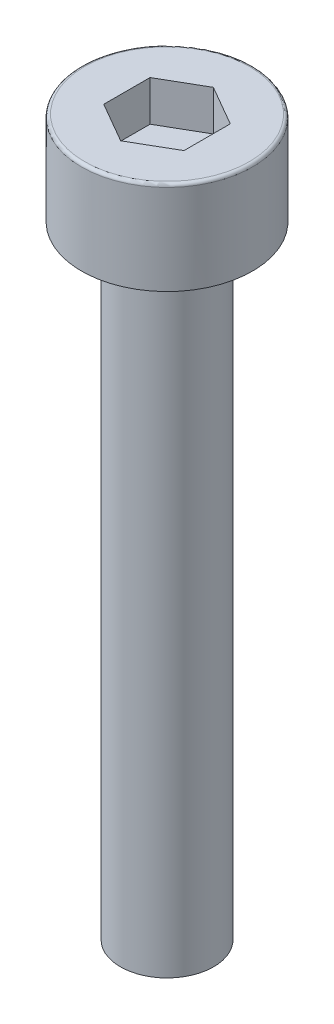
SolidWorks part; units mm, degrees
ref_plane "Front Plane" through (0, 0, 0) normal (0, 0, 1) x (1, 0, 0)
ref_plane "Top Plane" through (0, 0, 0) normal (0, 1, 0) x (1, 0, 0)
ref_plane "Right Plane" through (0, 0, 0) normal (1, 0, 0) x (0, 0, -1)
sketch "Sketch1" plane through (0, 0, 0) normal (0, 0, 1) x (1, 0, 0)
  line L0 (0, 0) -> (0, 23)
  line L1 (0, 23) -> (2.75, 23)
  line L2 (2.75, 23) -> (2.75, 20)
  line L3 (2.75, 20) -> (1.5, 20)
  line L4 (1.5, 20) -> (1.5, 0)
  line L5 (1.5, 0) -> (0, 0)
  dimension "D1" = 1.5
  dimension "D2" = 20
  dimension "D3" = 2.75
  dimension "D4" = 3
revolve "Revolve1" add sketch "Sketch1" angle 360 about L0
sketch "Sketch2" plane through (0, 23, 0) normal (0, 1, 0) x (1, 0, 0)
  line L1 (0, 1.4896) -> (-1.29, 0.7448)
  line L2 (-1.29, 0.7448) -> (-1.29, -0.7448)
  line L3 (-1.29, -0.7448) -> (0, -1.4896)
  line L4 (0, -1.4896) -> (1.29, -0.7448)
  line L5 (1.29, -0.7448) -> (1.29, 0.7448)
  line L6 (1.29, 0.7448) -> (0, 1.4896)
  circle A0 centre (0, 0) radius 1.29 construction
  dimension "D1" = 2.58
extrude "Cut-Extrude1" cut sketch "Sketch2" against normal blind 1.3
fillet "Fillet1" radius 0.1 1 edges at (0, 23, -2.75)
